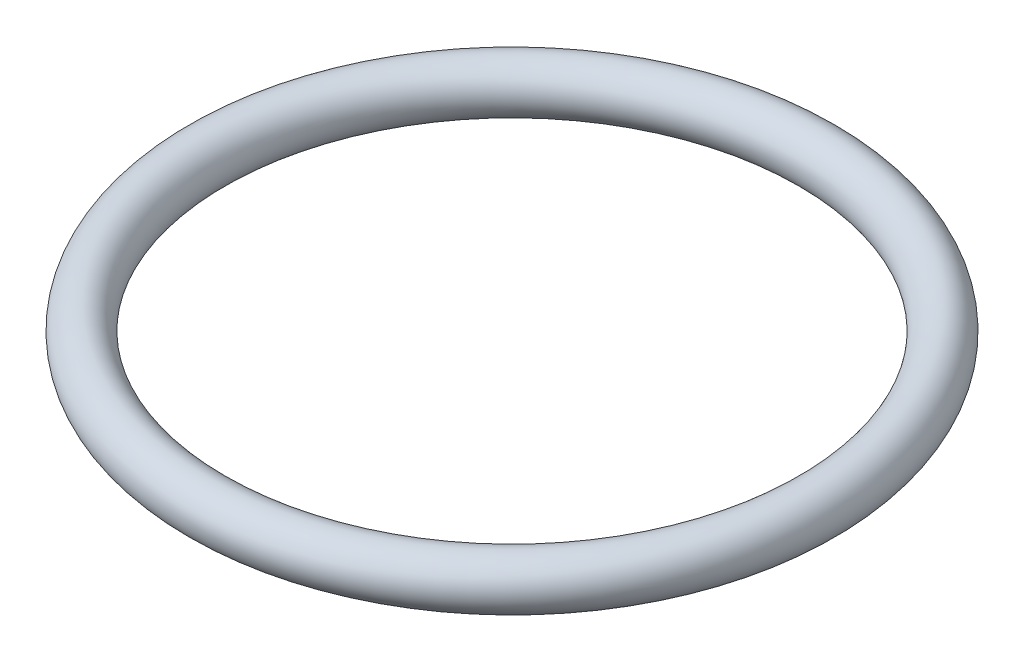
SolidWorks part; units mm, degrees
ref_plane "Front" through (0, 0, 0) normal (0, 0, 1) x (1, 0, 0)
ref_plane "Top" through (0, 0, 0) normal (0, 1, 0) x (1, 0, 0)
ref_plane "Right" through (0, 0, 0) normal (1, 0, 0) x (0, 0, -1)
sketch "Sketch3" plane through (0, 0, 0) normal (0, 0, 1) x (1, 0, 0)
  line L0 (0, 0) -> (0, 3.5934) construction
  circle A0 centre (8.5, 0) radius 0.7
  dimension "D2" = 1.4
  dimension "D1" = 8.5
revolve "Revolve1" add sketch "Sketch3" angle 360 about L0
